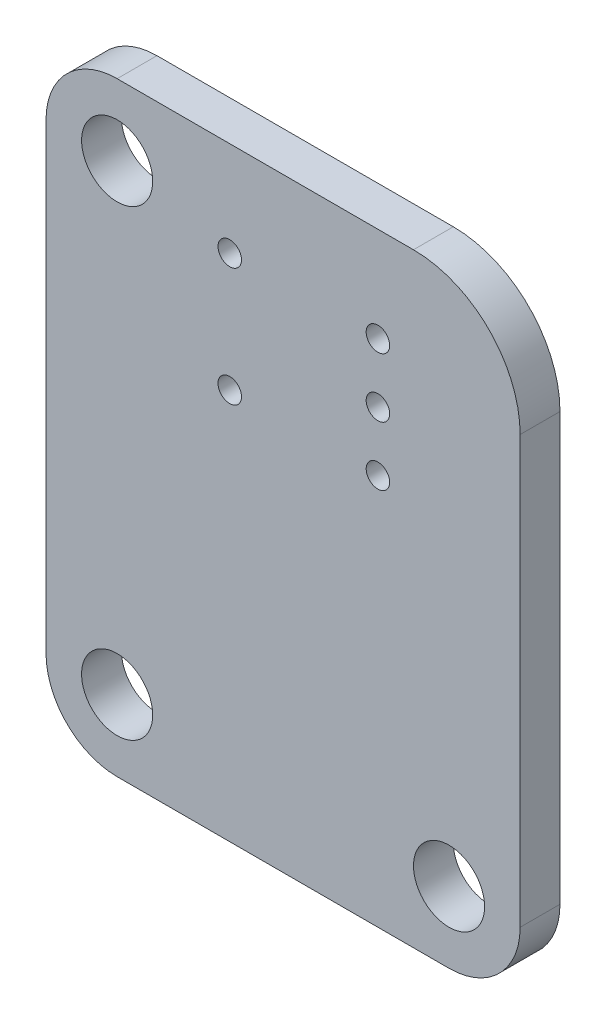
SolidWorks part; units mm, degrees
ref_plane "Front Plane" through (0, 0, 0) normal (0, 0, 1) x (1, 0, 0)
ref_plane "Top Plane" through (0, 0, 0) normal (0, 1, 0) x (1, 0, 0)
ref_plane "Right Plane" through (0, 0, 0) normal (1, 0, 0) x (0, 0, -1)
sketch "Sketch1" plane through (0, 0, -4.7) normal (0, 0, 1) x (1, 0, 0)
  line L0 (82.5, 65) -> (4.5, 65) construction
  line L1 (100, 26.864) -> (100, 37.5) construction
  line L2 (100, 42.5) -> (100, 60.5)
  line L3 (95.5, 65) -> (83, 65)
  line L4 (97, 39.5) -> (83, 39.5)
  line L5 (80, 42.5) -> (80, 62)
  arc A0 (100.5, 60.5) -> (95.5, 65.5) centre (95.5, 60.5) ccw construction
  arc A1 (83, 45.5) -> (83, 39.5) centre (83, 42.5) ccw construction
  arc A3 (100, 60.5) -> (95.5, 65) centre (95.5, 60.5) ccw
  arc A4 (83, 65) -> (80, 62) centre (83, 62) ccw
  arc A6 (83, 39.5) -> (80, 42.5) centre (83, 42.5) cw
  arc A7 (97, 39.5) -> (100, 42.5) centre (97, 42.5) ccw
  arc A18 (83, 59) -> (85.9468, 61.4375) centre (83, 62) ccw construction
  arc A19 (83, 59) -> (85.9468, 61.4375) centre (83, 62) ccw construction
extrude "BOARD" add sketch "Sketch1" along normal blind 1.68 separate body
sketch "Sketch2" plane through (0, 0, 0) normal (0, 0, 1) x (1, 0, 0)
  circle A0 centre (83, 42.5) radius 1.5
  circle A1 centre (97, 42.5) radius 1.5
  circle A2 centre (97, 35.5) radius 1.5
  circle A6 centre (83, 62) radius 1.5
  circle A7 centre (87.75, 56) radius 0.4953
  circle A8 centre (87.75, 61) radius 0.4953
  circle A9 centre (94, 58.5) radius 0.4953
  circle A10 centre (94, 56) radius 0.4953
  circle A11 centre (94, 61) radius 0.4953
  dimension "D1" = 3
extrude "PLATED HOLES" cut sketch "Sketch2" against normal through all
ref_plane "Plane1" through (0, 0, 0.8992) normal (0, 0, 1) x (1, 0, 0)
sketch "Sketch3" plane through (0, 0, 0) normal (0, 0, 1) x (1, 0, 0)
  line L0 (85.6, 63.45) -> (100.1, 63.45)
  line L1 (100.1, 63.45) -> (100.1, 53.55)
  line L2 (100.1, 53.55) -> (85.6, 53.55)
  line L3 (85.6, 53.55) -> (85.6, 63.45)
extrude "ENCODER_PEC09-2320F-S0015-1" [suppressed] add sketch "Sketch3" against normal blind 0.0254 separate body
sketch "Sketch4" plane through (0, 0, -3.02) normal (0, 0, 1) x (1, 0, 0)
  line L1 (86.2, 62) -> (99.5, 62)
  line L2 (86.2, 62) -> (86.2, 52.3)
  line L3 (86.2, 52.3) -> (99.5, 52.3)
  line L4 (99.5, 62) -> (99.5, 52.3)
  line L5 (87.2, 51.3) -> (93.2, 51.3)
  line L6 (87.2, 51.3) -> (87.2, 43.3)
  line L7 (87.2, 43.3) -> (93.2, 43.3)
  line L8 (93.2, 51.3) -> (93.2, 43.3)
